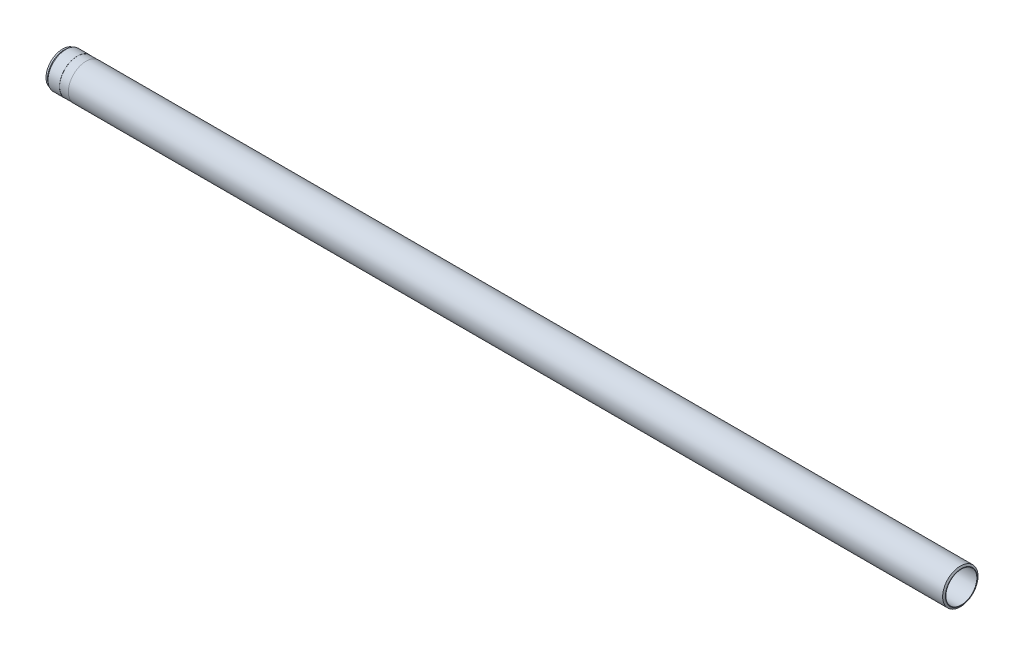
SolidWorks part; units mm, degrees
ref_plane "Front" through (0, 0, 0) normal (0, 0, 1) x (1, 0, 0)
ref_plane "Top" through (0, 0, 0) normal (0, 1, 0) x (1, 0, 0)
ref_plane "Right" through (0, 0, 0) normal (1, 0, 0) x (0, 0, -1)
sketch "Sketch1" plane through (0, 0, 0) normal (0, 0, 1) x (1, 0, 0)
  line L0 (-122.7842, 0) -> (99.5499, 0) construction
  line L1 (0, 35) -> (0, 36)
  line L2 (0, 36) -> (-2.3094, 40)
  line L3 (-2.3094, 40) -> (-1978, 40)
  line L4 (-1978, 40) -> (-1978, 39.75)
  line L5 (-1978, 39.75) -> (-1998, 39.75)
  line L6 (-1998, 39.75) -> (-1998, 40)
  line L7 (-1998, 40) -> (-2023.9296, 40)
  line L8 (-2023.9296, 40) -> (-2027.5, 37.5)
  line L9 (-2027.5, 37.5) -> (-2031, 37.5)
  line L10 (-2031, 37.5) -> (-2031, 35.7274)
  line L11 (-2031, 35.7274) -> (-2030, 35.15)
  line L12 (-2030, 35.15) -> (-2016, 35.15)
  line L13 (-2016, 35.15) -> (-2015.7402, 35)
  line L14 (-2015.7402, 35) -> (0, 35)
  dimension "D1" = 2031
  dimension "D2" = 80
  dimension "D3" = 70
  dimension "D4" = 70.3
  dimension "D5" = 75
  dimension "D6" = 72
  dimension "D7" = 60
  dimension "D8" = 79.5
  dimension "D9" = 3.5
  dimension "D10" = 35
  dimension "D11" = 30
  dimension "D12" = 1
  dimension "D13" = 30
  dimension "D14" = 15
  dimension "D15" = 33
  dimension "D16" = 20
revolve "Base-Revolve" add sketch "Sketch1" angle 360 about L0
